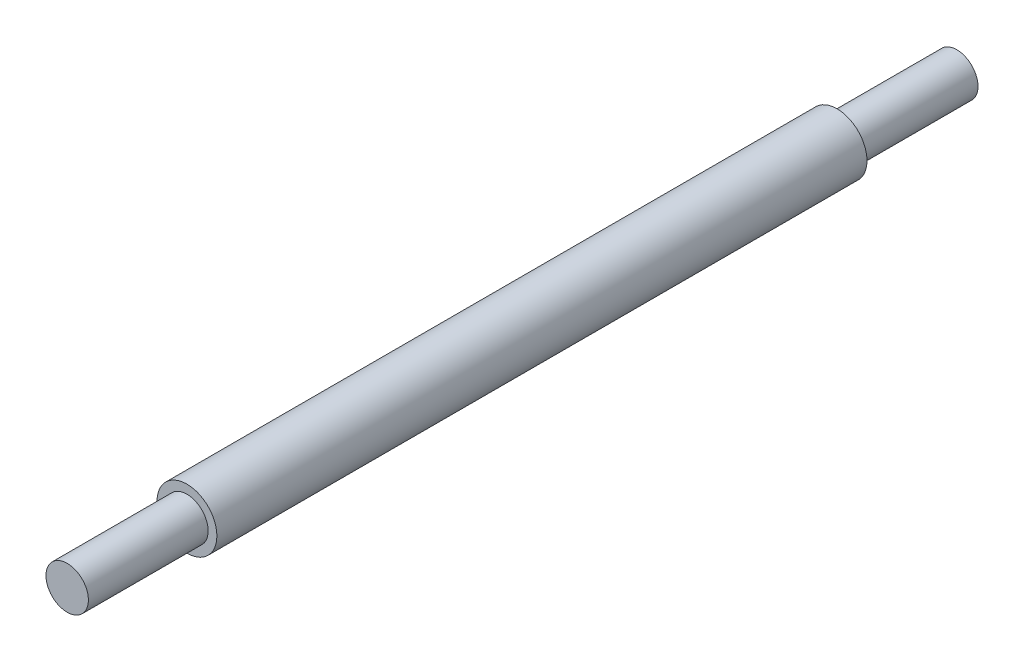
SolidWorks part; units mm, degrees
ref_plane "Front Plane" through (0, 0, 0) normal (0, 0, 1) x (1, 0, 0)
ref_plane "Top Plane" through (0, 0, 0) normal (0, 1, 0) x (1, 0, 0)
ref_plane "Right Plane" through (0, 0, 0) normal (1, 0, 0) x (0, 0, -1)
sketch "Sketch2" plane through (0, 0, 0) normal (0, 0, 1) x (1, 0, 0)
  circle A0 centre (0, 0) radius 2.7781
  dimension "D1" = 5.5562
extrude "Extrude1" add sketch "Sketch2" along normal mid plane 60.325
sketch "Sketch3" plane through (0, 0, 30.1625) normal (0, 0, 1) x (1, 0, 0)
  circle A0 centre (0, 0) radius 1.9685
  dimension "D1" = 3.937
extrude "Extrude2" add sketch "Sketch3" along normal blind 11.1125
sketch "Sketch4" plane through (0, 0, -30.1625) normal (0, 0, -1) x (-1, 0, 0)
  circle A0 centre (0, 0) radius 1.9685
  dimension "D1" = 3.937
extrude "Extrude3" add sketch "Sketch4" along normal blind 11.1125
